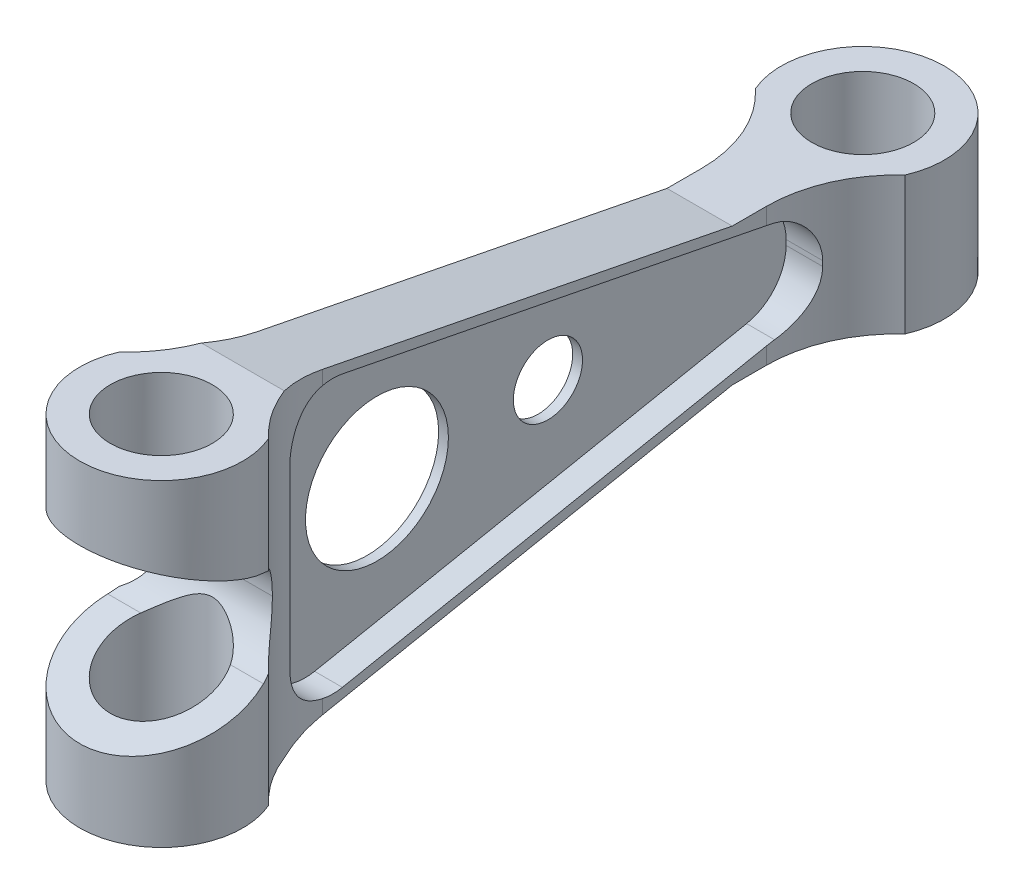
SolidWorks part; units mm, degrees
ref_plane "Front Plane" through (0, 0, 0) normal (0, 0, 1) x (1, 0, 0)
ref_plane "Top Plane" through (0, 0, 0) normal (0, 1, 0) x (1, 0, 0)
ref_plane "Right Plane" through (0, 0, 0) normal (1, 0, 0) x (0, 0, -1)
sketch "Sketch2" plane through (0, 0, 0) normal (0, 1, 0) x (1, 0, 0)
  line L0 (0, 0) -> (0, -273.05) construction
  line L1 (-12.7, -222.9704) -> (-12.7, -29.0994)
  line L2 (12.7, -222.9704) -> (12.7, -29.0994)
  arc A0 (-19.1322, -25.3381) -> (-29.0994, -12.7) centre (0, 0) ccw
  circle A1 centre (0, 0) radius 19.8438
  arc A2 (-12.7, -50.0796) -> (-29.0994, -12.7) centre (-63.5, -50.0796) ccw
  arc A3 (-29.0994, -260.35) -> (29.0994, -260.35) centre (0, -273.05) ccw
  arc A4 (-29.0994, -260.35) -> (-12.7, -222.9704) centre (-63.5, -222.9704) ccw
  circle A5 centre (0, -273.05) radius 19.8438
  arc A6 (29.0994, -260.35) -> (12.7, -222.9704) centre (63.5, -222.9704) cw
  arc A7 (12.7, -50.0796) -> (29.0994, -12.7) centre (63.5, -50.0796) cw
  point P4 (-29.0994, -12.7)
  point P8 (-29.0994, -260.35)
  dimension "D1" = 63.5
  dimension "D2" = 39.6875
  dimension "D4" = 12.7
  dimension "D5" = 63.5
  dimension "D8" = 101.6
  dimension "D9" = 101.6
  dimension "D10" = 39.6875
  dimension "D3" = 12.7
  dimension "D6" = 273.05
  dimension "D7" = 12.7
extrude "Boss-Extrude1" add sketch "Sketch2" along normal blind 123.698
sketch "Sketch3" plane through (0, 0, 0) normal (1, 0, 0) x (0, 0, -1)
  line L0 (-241.3, 123.698) -> (-63.5, 88.646)
  line L1 (-222.9704, 123.698) -> (-260.35, 123.698) construction
  line L2 (-250.952, 62.5797) -> (-250.952, 61.1183)
  line L3 (-273.05, 123.698) -> (-273.05, 0) construction
  line L4 (-12.7, 123.698) -> (-12.7, 0) construction
  line L5 (-304.8, 61.849) -> (31.75, 61.849) construction
  line L6 (-304.8, 123.698) -> (-304.8, 0) construction
  line L7 (31.75, 0) -> (31.75, 123.698) construction
  line L8 (-241.3, 123.698) -> (31.75, 123.698)
  line L9 (31.75, 123.698) -> (-12.7, 123.698) construction
  line L10 (31.75, 123.698) -> (31.75, 88.646)
  line L11 (31.75, 88.646) -> (-63.5, 88.646)
  line L12 (31.75, 0) -> (31.75, 35.052)
  line L13 (-241.3, 0) -> (31.75, 0)
  line L14 (-241.3, 0) -> (-63.5, 35.052)
  line L15 (31.75, 35.052) -> (-63.5, 35.052)
  line L16 (-304.8, 123.698) -> (-304.8, 95.25)
  line L17 (-304.8, 95.25) -> (-263.5894, 80.518)
  line L19 (-304.8, 0) -> (-304.8, 28.448)
  line L20 (-304.8, 28.448) -> (-263.5894, 43.18)
  line L21 (-304.8, 28.448) -> (-304.8, 95.25)
  circle A0 centre (-191.008, 61.849) radius 27.813
  circle A1 centre (-124.46, 61.849) radius 13.462
  circle A2 centre (-270.002, 62.5797) radius 19.05
  circle A3 centre (-270.002, 61.1183) radius 19.05
  dimension "D5" = 55.626
  dimension "D6" = 26.924
  dimension "D11" = 38.1
  dimension "D1" = 31.75
  dimension "D2" = 50.8
  dimension "D3" = 26.797
  dimension "D4" = 66.548
  dimension "D7" = 82.042
  dimension "D8" = 28.448
  dimension "D9" = 43.18
  dimension "D10" = 22.098
extrude "Cut-Extrude1" cut sketch "Sketch3" against normal through all both and the other way through all contours A3 L5 | L5 A2 | A3 A2 | L5 L21 L20 A3 | L21 L5 A2 L17 | A2 A3 | A0 L5 | L11 L10 L8 L0 | L12 L15 L14 L13 | L5 A0 | L5 A1 | A1 L5
sketch "Sketch4" plane through (12.7, 0, 0) normal (1, 0, 0) x (0, 0, -1)
  line L0 (-215.2633, 114.6817) -> (-47.1153, 81.5326)
  line L1 (-237.998, 61.849) -> (31.5249, 61.849) construction
  line L2 (-63.5, 88.646) -> (-222.9704, 120.0844) construction
  line L3 (-31.75, 62.8423) -> (-31.75, 60.8557)
  line L4 (-273.05, 141.5929) -> (-273.05, 87.9083) construction
  line L5 (-237.998, 95.9915) -> (-237.998, 27.7065)
  line L6 (-215.2633, 9.0163) -> (-47.1153, 42.1654)
  line L7 (-63.5, 35.052) -> (-222.9704, 3.6136) construction
  line L10 (0, 88.646) -> (0, 35.052) construction
  arc A0 (-47.1153, 42.1654) -> (-31.75, 60.8557) centre (-50.8, 60.8557) ccw
  arc A1 (-237.998, 27.7065) -> (-215.2633, 9.0163) centre (-218.948, 27.7065) ccw
  arc A2 (-215.2633, 114.6817) -> (-237.998, 95.9915) centre (-218.948, 95.9915) ccw
  arc A3 (-47.1153, 81.5326) -> (-31.75, 62.8423) centre (-50.8, 62.8423) cw
  point P21 (-237.998, 119.1637)
  point P25 (-31.75, 78.5034)
  circle M7 centre (-124.46, 61.849) radius 13.462
  circle M8 centre (-191.008, 61.849) radius 27.813
  line M11 (-50.0796, 35.052) -> (-50.0796, 88.646)
  line M14 (-222.9704, 120.0844) -> (-222.9704, 3.6136)
  dimension "D5" = 31.75
  dimension "D4" = 19.05
  dimension "D6" = 19.05
  dimension "D1" = 3.81
  dimension "D2" = 35.052
  dimension "D3" = 3.81
extrude "Cut-Extrude2" cut sketch "Sketch4" against normal blind 10.795 and the other way through all contours L1 L0 A2 M14 M8 M7 M11 | L5 L1 A2 M14 | L1 L5 A1 M14 | L1 A1 L6 M14 M11 M7 M8 | L1 L6 A0 L3 M11 | L1 L3 A3 L0 M11
mirror "Mirror1" about plane through (0, 0, 0) normal (1, 0, 0) of "Cut-Extrude2"
